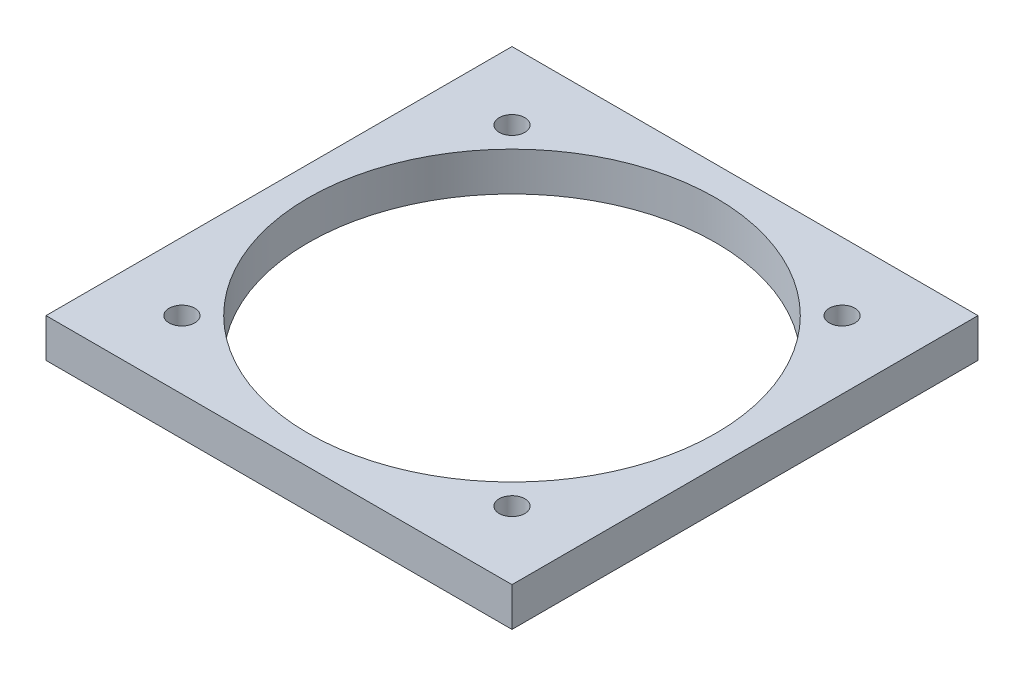
SolidWorks part; units mm, degrees
ref_plane "Front Plane" through (0, 0, 0) normal (0, 0, 1) x (1, 0, 0)
ref_plane "Top Plane" through (0, 0, 0) normal (0, 1, 0) x (1, 0, 0)
ref_plane "Right Plane" through (0, 0, 0) normal (1, 0, 0) x (0, 0, -1)
sketch "Sketch1" plane through (0, 0, 0) normal (0, 1, 0) x (1, 0, 0)
  line L1 (-26.9875, -26.9875) -> (26.9875, -26.9875)
  line L2 (-26.9875, -26.9875) -> (-26.9875, 26.9875)
  line L3 (-26.9875, 26.9875) -> (26.9875, 26.9875)
  line L4 (26.9875, -26.9875) -> (26.9875, 26.9875)
  line L5 (-26.9875, -26.9875) -> (26.9875, 26.9875) construction
  line L6 (-26.9875, 26.9875) -> (26.9875, -26.9875) construction
  line L7 (38.1, 38.1) -> (-38.1, 38.1)
  line L8 (38.1, 38.1) -> (38.1, -38.1)
  line L9 (38.1, -38.1) -> (-38.1, -38.1)
  line L10 (-38.1, 38.1) -> (-38.1, -38.1)
  line L11 (38.1, 38.1) -> (-38.1, -38.1) construction
  line L12 (38.1, -38.1) -> (-38.1, 38.1) construction
  circle A0 centre (0, 0) radius 33.3375
  circle A1 centre (26.9875, 26.9875) radius 2.0955
  circle A2 centre (-26.9875, 26.9875) radius 2.0955
  circle A3 centre (-26.9875, -26.9875) radius 2.0955
  circle A4 centre (26.9875, -26.9875) radius 2.0955
  dimension "D1" = 66.675
  dimension "D4" = 4.191
  dimension "D5" = 4.191
  dimension "D6" = 4.191
  dimension "D2" = 53.975
  dimension "D3" = 53.975
  dimension "D7" = 76.2
  dimension "D8" = 76.2
extrude "Boss-Extrude1" add sketch "Sketch1" along normal blind 6.35 contours L7 L10 L9 L8 A4 L1 A0 A3 L2 A2 L3 A1 L4 | A3 L1 A0 L2 | A4 L4 A0 L1 | A1 L3 A0 L4 | A2 L2 A0 L3
